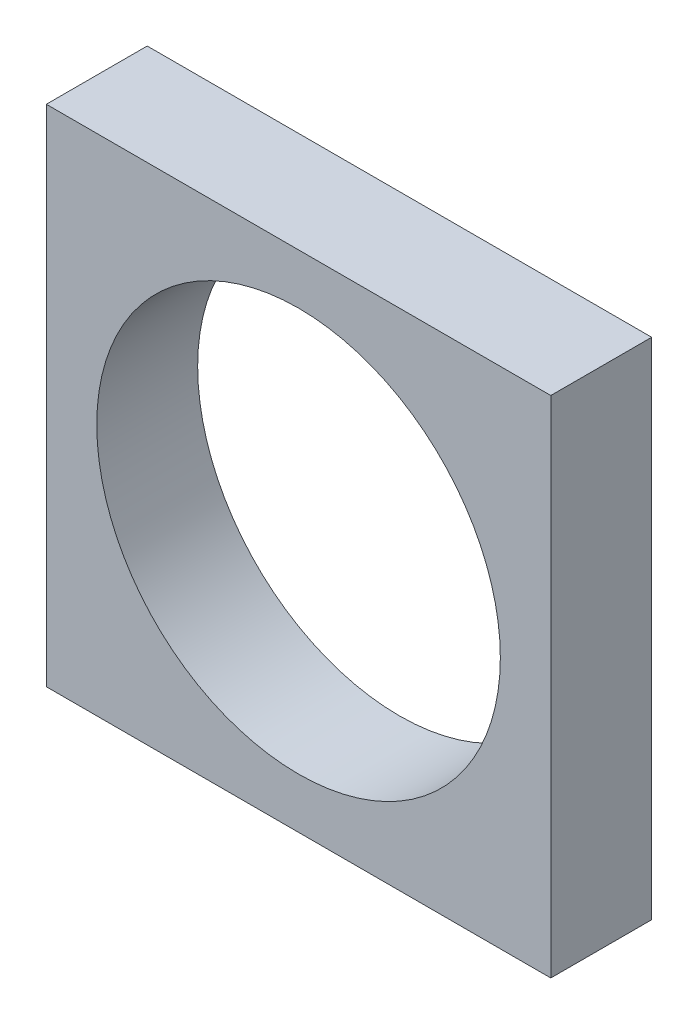
SolidWorks part; units mm, degrees
ref_plane "Front Plane" through (0, 0, 0) normal (0, 0, 1) x (1, 0, 0)
ref_plane "Top Plane" through (0, 0, 0) normal (0, 1, 0) x (1, 0, 0)
ref_plane "Right Plane" through (0, 0, 0) normal (1, 0, 0) x (0, 0, -1)
sketch "Sketch1" plane through (0, 0, 0) normal (0, 0, 1) x (1, 0, 0)
  line L1 (-50, 50) -> (50, 50)
  line L2 (-50, 50) -> (-50, -50)
  line L3 (-50, -50) -> (50, -50)
  line L4 (50, 50) -> (50, -50)
  line L5 (-50, 50) -> (50, -50) construction
  line L6 (-50, -50) -> (50, 50) construction
  point P0 (0, 0)
  dimension "D1" = 100
  dimension "D2" = 100
extrude "Boss-Extrude1" add sketch "Sketch1" along normal blind 20
sketch "Sketch2" plane through (0, 0, 20) normal (0, 0, 1) x (1, 0, 0)
  circle A0 centre (0, 0) radius 40
  dimension "D1" = 80
extrude "Cut-Extrude1" cut sketch "Sketch2" against normal blind 20
equation "\"Sketch2\"= \"d\""
equation "\"d\"= 50"
